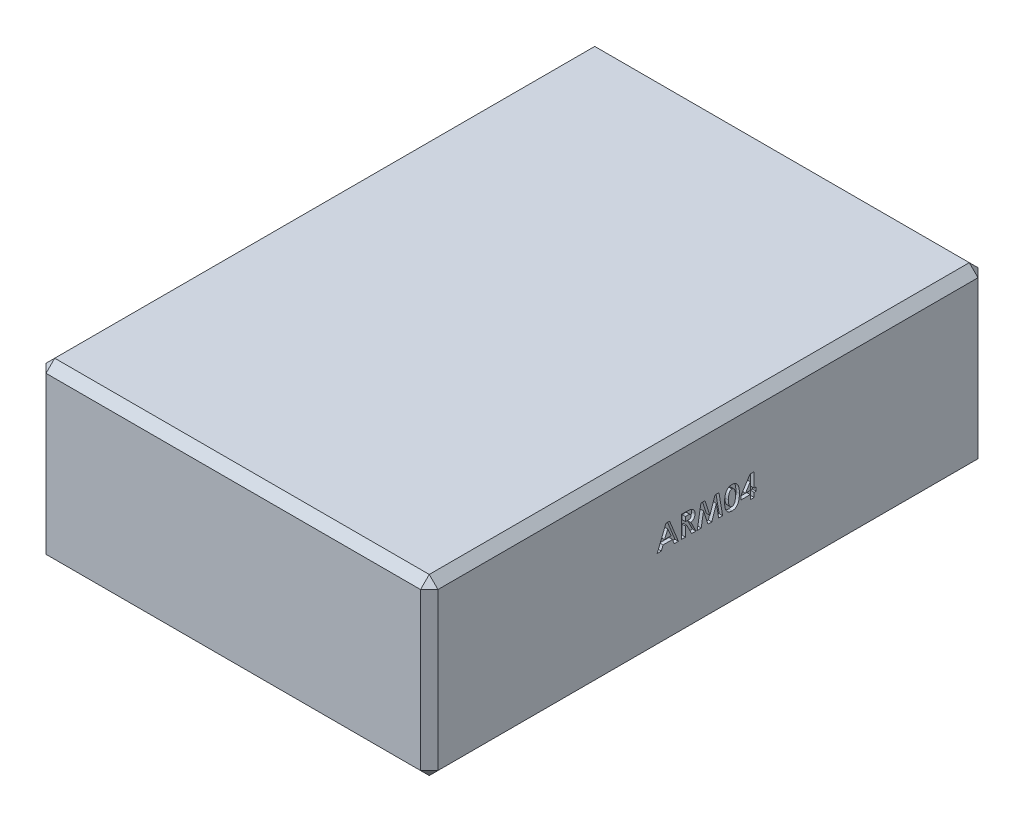
SolidWorks part; units mm, degrees
material "PET"
ref_plane "Front Plane" through (0, 0, 0) normal (0, 0, 1) x (1, 0, 0)
ref_plane "Top Plane" through (0, 0, 0) normal (0, 1, 0) x (1, 0, 0)
ref_plane "Right Plane" through (0, 0, 0) normal (1, 0, 0) x (0, 0, -1)
sketch "Sketch2" plane through (0, 0, 0) normal (0, 0, 1) x (1, 0, 0)
  line L1 (-28.575, 0) -> (28.575, 0)
  line L2 (-28.575, 0) -> (-28.575, 25.4)
  line L3 (-28.575, 25.4) -> (28.575, 25.4)
  line L4 (28.575, 0) -> (28.575, 25.4)
  point P4 (0, 0)
  dimension "D1" = 57.15
  dimension "D2" = 25.4
extrude "Boss-Extrude1" add sketch "Sketch2" against normal blind 81.28
sketch "Sketch4" plane through (0, 0, -81.28) normal (0, 0, -1) x (-1, 0, 0)
  line L6 (-7.0218, 0) -> (7.0218, 0)
  line L14 (6.3237, 1.0674) -> (10.3017, 10.16)
  line L15 (10.3017, 10.16) -> (-10.3017, 10.16)
  line L16 (-10.3017, 10.16) -> (-6.3237, 1.0674)
  line L17 (0, 0) -> (0, 10.16) construction
  arc A2 (6.3237, 1.0674) -> (7.0218, 0) centre (7.0218, 0.762) ccw
  arc A3 (-7.0218, 0) -> (-6.3237, 1.0674) centre (-7.0218, 0.762) ccw
  point P2 (0, 0)
  point P3 (0, 0)
  point P4 (0, 0)
  point P9 (0, 0)
  point P16 (-6.3478, 1.5175)
  point P19 (0, 0)
  point P20 (-10.3017, 10.16)
  point P21 (-5.5329, 2.1609)
  point P22 (0, 0)
  point P23 (0, 0)
  point P24 (6.2471, 1.201)
  dimension "D5" = 0.762
  dimension "D1" = 20.6035
  dimension "D2" = 14.0437
  dimension "D3" = 10.16
extrude "Cut-Extrude1" cut sketch "Sketch4" against normal blind 78.74
chamfer "Chamfer1" distance 1.27 angle 45 11 edges at (-28.575, 12.7, -81.28) (-28.575, 12.7, 0) (28.575, 12.7, -81.28) (-28.575, 0, -40.64) (0, 0, 0) (28.575, 0, -40.64) (28.575, 12.7, 0) (-28.575, 25.4, -40.64) (0, 25.4, -81.28) (28.575, 25.4, -40.64) (0, 25.4, 0)
sketch "Sketch5" plane through (28.575, 0, 0) normal (1, 0, 0) x (0, 0, -1)
  line L0 (0, 12.7) -> (81.28, 12.7) construction
  line L3 (0, 1.27) -> (0, 24.13) construction
  line L4 (81.28, 1.27) -> (81.28, 24.13) construction
  text T0 "<b>ARM04</b>"
  point P9 (81.28, 12.7)
extrude "Cut-Extrude2" cut sketch "Sketch5" against normal blind 0.508
sketch "Sketch6" plane through (-28.575, 0, 0) normal (-1, 0, 0) x (0, 0, 1)
  line L0 (-81.28, 12.7) -> (0, 12.7) construction
  line L3 (-81.28, 24.13) -> (-81.28, 1.27) construction
  line L4 (0, 24.13) -> (0, 1.27) construction
  text T0 "<b>ARM04</b>"
  point P4 (-81.28, 12.7)
extrude "Cut-Extrude3" cut sketch "Sketch6" against normal blind 0.508
chamfer "Chamfer2" distance 0.508 angle 45 7 edges at (-17.1634, 0, -81.28) (17.1634, 0, -81.28) (-6.3841, 0.3449, -81.28) (6.3841, 0.3449, -81.28) (-8.3127, 5.6137, -81.28) (0, 10.16, -81.28) (8.3127, 5.6137, -81.28)
